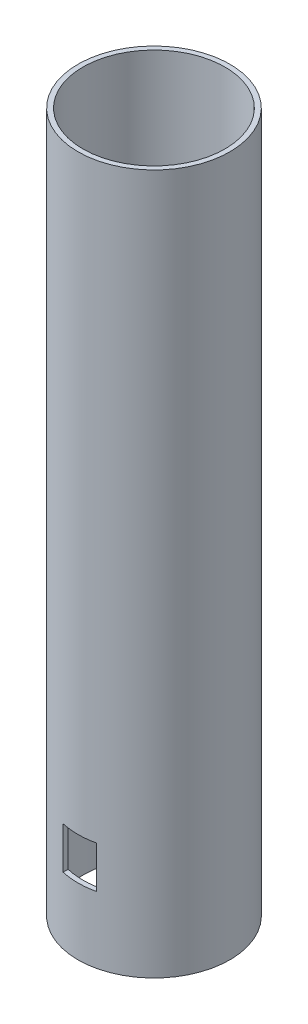
SolidWorks part; units mm, degrees
ref_plane "Front Plane" through (0, 0, 0) normal (0, 0, 1) x (1, 0, 0)
ref_plane "Top Plane" through (0, 0, 0) normal (0, 1, 0) x (1, 0, 0)
ref_plane "Right Plane" through (0, 0, 0) normal (1, 0, 0) x (0, 0, -1)
sketch "Sketch1" plane through (0, 0, 0) normal (0, 1, 0) x (1, 0, 0)
  circle A0 centre (0, 0) radius 27.125
  circle A1 centre (0, 0) radius 25.375
  dimension "Outer_Dia" = 54.25
  dimension "Inner_Dia" = 50.75
extrude "Boss-Extrude1" add sketch "Sketch1" along normal mid plane 250
sketch "Sketch3" plane through (0, 0, 0) normal (0, 0, 1) x (1, 0, 0)
  line L0 (-27.125, -125) -> (27.125, -125) construction
  line L1 (1, -65) -> (-1, -65)
  line L2 (1, -65) -> (1, -125)
  line L3 (1, -125) -> (-1, -125)
  line L4 (-1, -65) -> (-1, -125)
  line L5 (1, -65) -> (-1, -125) construction
  line L6 (1, -125) -> (-1, -65) construction
  point P0 (0, -95)
  dimension "D1" = 2
  dimension "D2" = 60
curve "Curve1"
sketch "Sketch4" plane through (0, 0, 0) normal (1, 0, 0) x (0, 0, -1)
  line L0 (-27.125, -125) -> (27.125, -125) construction
  line L1 (1, -65) -> (-1, -65)
  line L2 (1, -65) -> (1, -125)
  line L3 (1, -125) -> (-1, -125)
  line L4 (-1, -65) -> (-1, -125)
  line L5 (1, -65) -> (-1, -125) construction
  line L6 (1, -125) -> (-1, -65) construction
  point P0 (0, -95)
  dimension "D1" = 60
  dimension "D2" = 2
curve "Curve2"
sketch "Sketch5" plane through (0, 0, 0) normal (0, 0, 1) x (1, 0, 0)
  line L0 (-63.3621, -95) -> (63.3621, -95) construction
  line L1 (-27.125, -125) -> (27.125, -125) construction
  line L3 (-6, -101.2) -> (6, -101.2)
  line L4 (-6, -101.2) -> (-6, -86.2)
  line L5 (-6, -86.2) -> (6, -86.2)
  line L6 (6, -101.2) -> (6, -86.2)
  point P4 (0, -95)
  point P10 (0, -101.2)
  dimension "D1" = 30
  dimension "D2" = 6.2
  dimension "D3" = 15
  dimension "D4" = 12
extrude "Cut-Extrude1" cut sketch "Sketch5" against normal through all both and the other way through all
